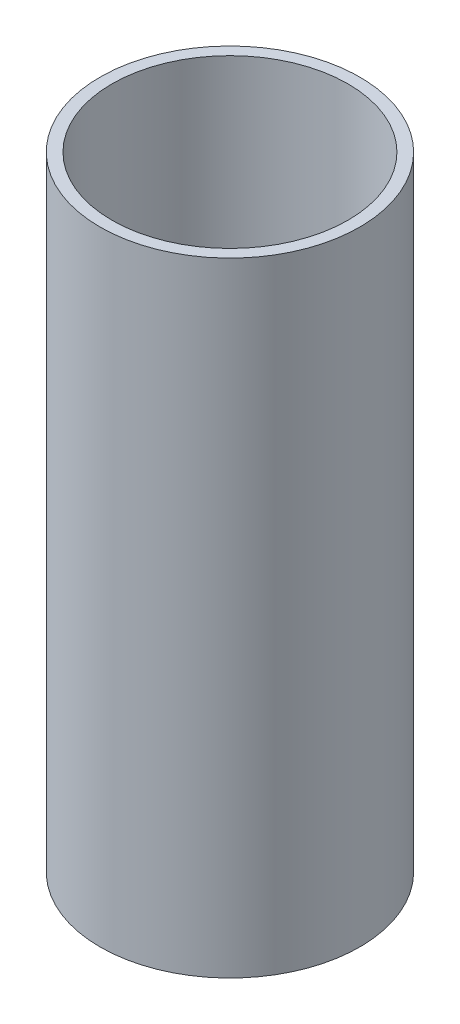
SolidWorks part; units mm, degrees
ref_plane "前视" through (0, 0, 0) normal (0, 0, 1) x (1, 0, 0)
ref_plane "上视" through (0, 0, 0) normal (0, 1, 0) x (1, 0, 0)
ref_plane "右视" through (0, 0, 0) normal (1, 0, 0) x (0, 0, -1)
sketch "草图1" plane through (0, 0, 0) normal (0, 1, 0) x (1, 0, 0)
  circle A0 centre (0, 0) radius 55
  circle A1 centre (0, 0) radius 50
  dimension "D1" = 110
  dimension "D3" = 100
  dimension "D2" = 5
extrude "凸台-拉伸1" add sketch "草图1" along normal blind 264
